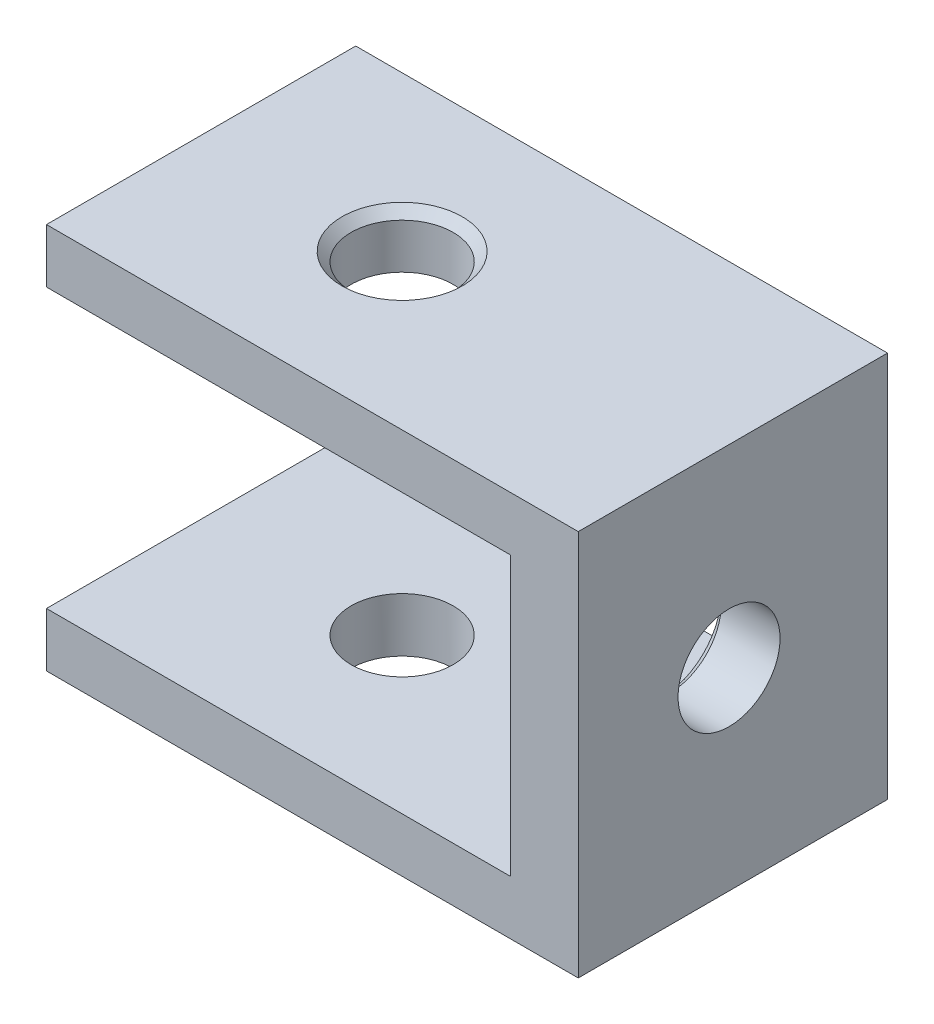
SolidWorks part; units mm, degrees
ref_plane "前视基准面" through (0, 0, 0) normal (0, 0, 1) x (1, 0, 0)
ref_plane "上视基准面" through (0, 0, 0) normal (0, 1, 0) x (1, 0, 0)
ref_plane "右视基准面" through (0, 0, 0) normal (1, 0, 0) x (0, 0, -1)
sketch "草图1" plane through (0, 0, 0) normal (0, 1, 0) x (1, 0, 0)
  line L1 (-49.3903, 10.2495) -> (70.6097, 10.2495)
  line L2 (-49.3903, 10.2495) -> (-49.3903, -9.7505)
  line L3 (-49.3903, -9.7505) -> (70.6097, -9.7505)
  line L4 (70.6097, 10.2495) -> (70.6097, -9.7505)
extrude "凸台-拉伸1" add sketch "草图1" along normal blind 25
sketch "草图2" plane through (-49.3903, 0, 0) normal (-1, 0, 0) x (0, 0, 1)
  line L0 (-10.2495, 12.5) -> (-10.2495, 21.5)
  line L1 (-10.2495, 25) -> (-10.2495, 0) construction
  line L2 (-10.2495, 12.5) -> (-10.2495, 3.5)
  line L3 (-10.2495, 21.5) -> (9.7505, 21.5)
  line L4 (9.7505, 25) -> (9.7505, 0) construction
  line L5 (9.7505, 21.5) -> (9.7505, 3.5)
  line L6 (9.7505, 3.5) -> (-10.2495, 3.5)
extrude "切除-拉伸1" cut sketch "草图2" against normal blind 30
sketch "草图3" plane through (0, 0, 9.7505) normal (0, 0, 1) x (1, 0, 0)
  line L0 (0, 0) -> (0, 25)
  line L1 (-49.3903, 25) -> (70.6097, 25) construction
  line L2 (-49.3903, 0) -> (70.6097, 0) construction
  line L3 (-15, 0) -> (70.6097, 0)
  line L4 (-15, 0) -> (-15, 25)
  line L5 (-15, 25) -> (70.6097, 25)
  line L6 (70.6097, 0) -> (70.6097, 25)
  line L7 (-15, 25) -> (0, 25)
  line M6 (-49.3903, 0) -> (70.6097, 0)
  line M7 (70.6097, 0) -> (70.6097, 25)
  line M8 (70.6097, 25) -> (-49.3903, 25)
extrude "切除-拉伸2" cut sketch "草图3" against normal blind 30 contours L4 L0 M6 M8 | L0 M6 M7 M8
sketch "草图4" plane through (0, 25, 0) normal (0, 1, 0) x (1, 0, 0)
  line L0 (-49.3903, 0.2495) -> (-36.3903, 0.2495)
  line L1 (-49.3903, 10.2495) -> (-49.3903, -9.7505) construction
hole_wizard "G1/16 螺纹孔1" positions "草图7" profile "草图8" tap size "G1/16" standard "GB"
sketch "草图7" plane through (0, 25, 0) normal (0, 1, 0) x (1, 0, 0)
  point P0 (-36.3903, 0.2495)
sketch "草图8" plane through (-36.3903, 25, -0.2495) normal (1, 0, 0) x (0, 0, 1)
  line L0 (0, 0) -> (0, 31.9828)
  line L1 (0, 31.9828) -> (3.3, 30)
  line L2 (3.3, 30) -> (3.3, 0.5865)
  line L3 (3.3, 0.5865) -> (3.8865, 0)
  line L5 (3.8865, 0) -> (0, 0)
  line L6 (-3.3, 0.5865) -> (-3.8865, 0) construction
  line L10 (0, 31.9828) -> (-3.3, 30) construction
  line L11 (0, -6.35) -> (0, 107.95) construction
  dimension "螺纹孔钻头直径" = 6.6
  dimension "螺纹孔钻头深度" = 30
  dimension "近端锥形沉头孔直径" = 7.773
  dimension "近端锥形沉头孔角度" = 90
  dimension "导头角度" = 118
cosmetic thread "孔螺蚊线1" parameters "D1"=15.45, "D2"=7.723
hole_wizard "G1/16 螺纹孔2" positions "草图9" profile "草图10" tap size "G1/16" standard "GB"
sketch "草图9" plane through (-19.3903, 0, 0) normal (-1, 0, 0) x (0, 0, 1)
  point P0 (0, 12.5)
sketch "草图10" plane through (-19.3903, 12.5, 0) normal (0, 1, 0) x (0, 0, 1)
  line L0 (0, 0) -> (0, 31.9828)
  line L1 (0, 31.9828) -> (3.3, 30)
  line L2 (3.3, 30) -> (3.3, 0.5865)
  line L3 (3.3, 0.5865) -> (3.8865, 0)
  line L5 (3.8865, 0) -> (0, 0)
  line L6 (-3.3, 0.5865) -> (-3.8865, 0) construction
  line L10 (0, 31.9828) -> (-3.3, 30) construction
  line L11 (0, -6.35) -> (0, 107.95) construction
  dimension "螺纹孔钻头直径" = 6.6
  dimension "螺纹孔钻头深度" = 30
  dimension "近端锥形沉头孔直径" = 7.773
  dimension "近端锥形沉头孔角度" = 90
  dimension "导头角度" = 118
cosmetic thread "孔螺蚊线2" parameters "D1"=15.45, "D2"=7.723
